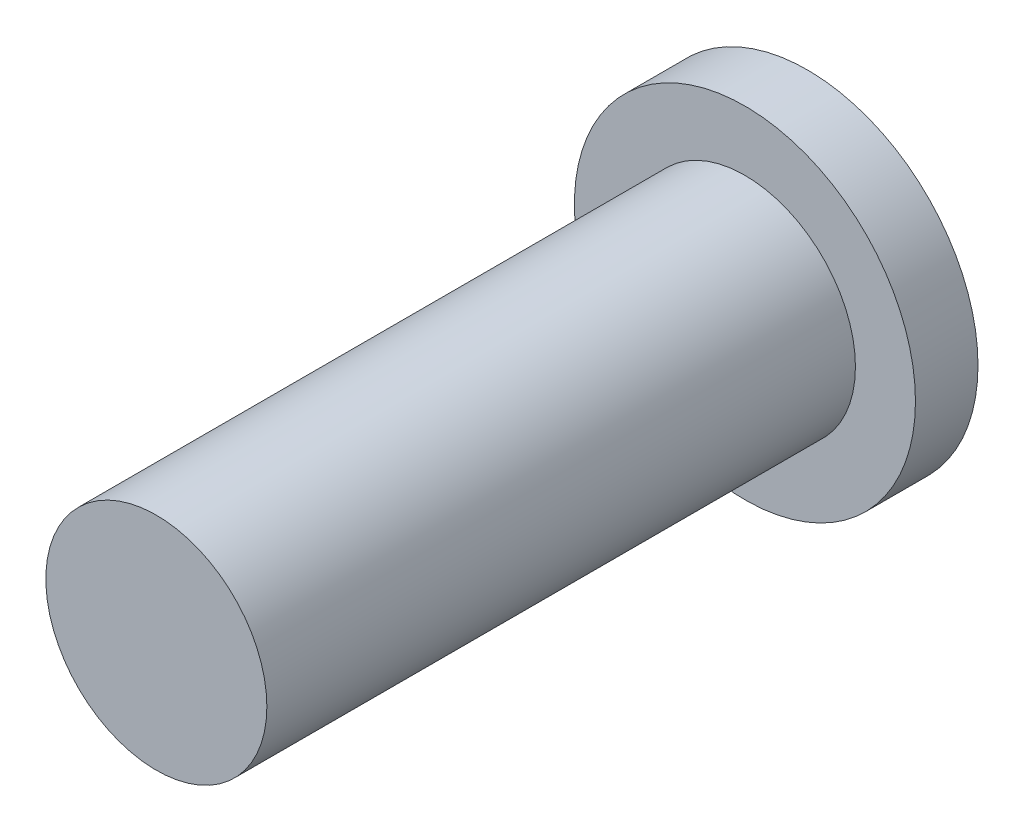
SolidWorks part; units mm, degrees
ref_plane "Front Plane" through (0, 0, 0) normal (0, 0, 1) x (1, 0, 0)
ref_plane "Top Plane" through (0, 0, 0) normal (0, 1, 0) x (1, 0, 0)
ref_plane "Right Plane" through (0, 0, 0) normal (1, 0, 0) x (0, 0, -1)
sketch "Sketch1" plane through (0, 0, 0) normal (0, 0, 1) x (1, 0, 0)
  circle A0 centre (0, 0) radius 231.8052
extrude "Boss-Extrude1" add sketch "Sketch1" along normal blind 85
sketch "Sketch2" plane through (0, 0, 85) normal (0, 0, 1) x (1, 0, 0)
  line L1 (-107.5751, 104.8401) -> (107.5751, 104.8401)
  line L2 (-107.5751, 104.8401) -> (-107.5751, -104.8401)
  line L3 (-107.5751, -104.8401) -> (107.5751, -104.8401)
  line L4 (107.5751, 104.8401) -> (107.5751, -104.8401)
  line L5 (-107.5751, 104.8401) -> (107.5751, -104.8401) construction
  line L6 (-107.5751, -104.8401) -> (107.5751, 104.8401) construction
  point P0 (0, 0)
extrude "Boss-Extrude3" add sketch "Sketch2" along normal blind 800
sketch "Sketch3" plane through (107.5751, 0, 0) normal (1, 0, 0) x (0, 0, -1)
  line L0 (0, 0) -> (-885, 0) construction
  line L1 (-885, -104.8401) -> (-885, 104.8401) construction
  circle A0 centre (-795.1848, 0) radius 35
  point P7 (0, 0)
extrude "Cut-Extrude1" cut sketch "Sketch3" against normal blind 248
sketch "Sketch4" plane through (0, 0, 885) normal (0, 0, 1) x (1, 0, 0)
  circle A0 centre (0, 0) radius 150.2127
extrude "Boss-Extrude5" add sketch "Sketch4" against normal up to vertex (885 mm away)
